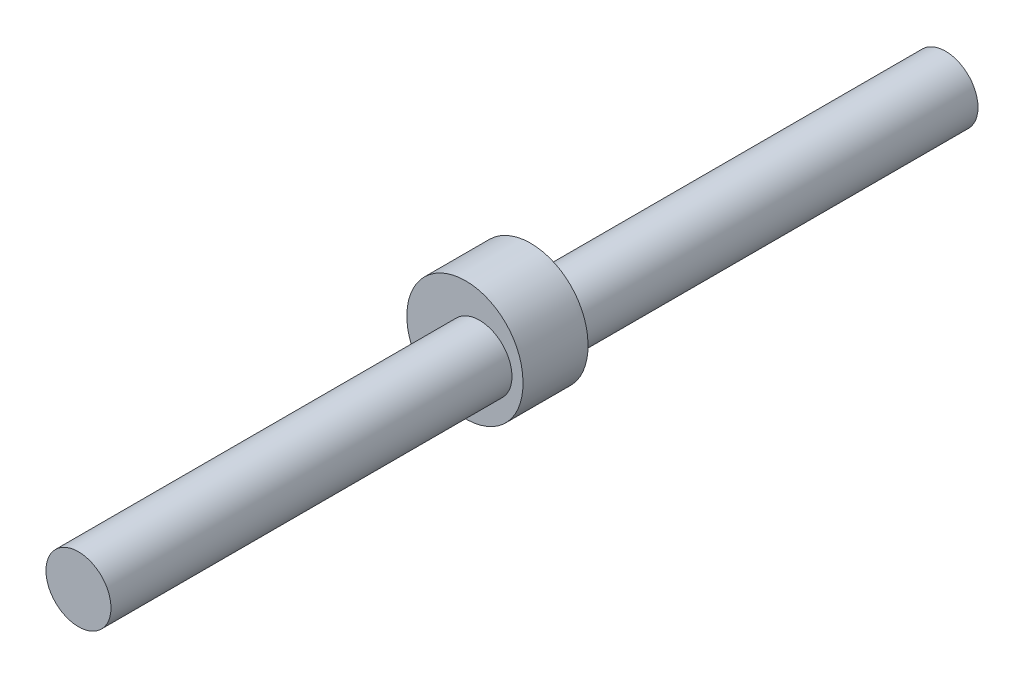
SolidWorks part; units mm, degrees
ref_plane "Front Plane" through (0, 0, 0) normal (0, 0, 1) x (1, 0, 0)
ref_plane "Top Plane" through (0, 0, 0) normal (0, 1, 0) x (1, 0, 0)
ref_plane "Right Plane" through (0, 0, 0) normal (1, 0, 0) x (0, 0, -1)
sketch "Sketch2" plane through (0, 0, 0) normal (0, 0, 1) x (1, 0, 0)
  spline S1 degree 3 poles (20.1005, -0.1773) (20.0999, -0.0008) (20.0997, 0.1756) (20.0981, 0.3513) (20.0956, 0.5269) (20.092, 0.7026) (20.0874, 0.8782) (20.0817, 1.0539) (20.0751, 1.2295) (20.0674, 1.4052) (20.0586, 1.5808) (20.0489, 1.7565) (20.0381, 1.9321) (20.0263, 2.1078) (20.0134, 2.2834) (19.9995, 2.4591) (19.9846, 2.6347) (19.9686, 2.8103) (19.9516, 2.986) (19.9335, 3.1616) (19.9144, 3.3372) (19.8942, 3.5128) (19.873, 3.6884) (19.8507, 3.864) (19.8273, 4.0396) (19.8029, 4.2152) (19.7775, 4.3908) (19.7509, 4.5664) (19.7233, 4.7419) (19.6946, 4.9175) (19.6648, 5.093) (19.6339, 5.2685) (19.6019, 5.444) (19.5689, 5.6194) (19.5347, 5.7949) (19.4994, 5.9703) (19.463, 6.1457) (19.4256, 6.321) (19.3869, 6.4964) (19.3472, 6.6717) (19.3063, 6.8469) (19.2643, 7.0221) (19.2212, 7.1973) (19.1769, 7.3724) (19.1314, 7.5475) (19.0848, 7.7225) (19.0371, 7.8975) (18.9881, 8.0724) (18.938, 8.2472) (18.8868, 8.422) (18.8343, 8.5967) (18.7806, 8.7713) (18.7258, 8.9458) (18.6697, 9.1203) (18.6126, 9.2947) (18.5529, 9.4702) (18.4951, 9.6468) (18.4343, 9.8209) (18.3699, 9.9923) (18.3078, 10.1649) (18.243, 10.3385) (18.1771, 10.512) (18.1099, 10.6854) (18.0415, 10.8587) (17.9717, 11.0318) (17.9007, 11.2048) (17.8284, 11.3776) (17.7548, 11.5502) (17.6799, 11.7226) (17.6037, 11.8948) (17.5262, 12.0669) (17.4474, 12.2387) (17.3673, 12.4103) (17.2858, 12.5817) (17.2029, 12.7529) (17.1188, 12.9238) (17.0332, 13.0945) (16.9463, 13.2649) (16.8581, 13.435) (16.7685, 13.6049) (16.6775, 13.7744) (16.5851, 13.9437) (16.4913, 14.1127) (16.3961, 14.2813) (16.2995, 14.4496) (16.2016, 14.6176) (16.1022, 14.7852) (16.0013, 14.9524) (15.8991, 15.1193) (15.7954, 15.2858) (15.6903, 15.4518) (15.5838, 15.6175) (15.4758, 15.7827) (15.3663, 15.9475) (15.2554, 16.1119) (15.1431, 16.2757) (15.0292, 16.4391) (14.9139, 16.602) (14.7971, 16.7644) (14.6789, 16.9263) (14.5591, 17.0877) (14.4379, 17.2484) (14.3152, 17.4087) (14.191, 17.5683) (14.0652, 17.7274) (13.938, 17.8858) (13.8093, 18.0437) (13.6791, 18.2009) (13.5473, 18.3574) (13.414, 18.5133) (13.2793, 18.6684) (13.143, 18.8229) (13.0051, 18.9767) (12.8658, 19.1297) (12.7249, 19.282) (12.5825, 19.4335) (12.4386, 19.5842) (12.2931, 19.7341) (12.1461, 19.8832) (11.9976, 20.0315) (11.8475, 20.1789) (11.6959, 20.3254) (11.5428, 20.4711) (11.3881, 20.6158) (11.2319, 20.7596) (11.0742, 20.9025) (10.915, 21.0444) (10.7542, 21.1853) (10.5919, 21.3253) (10.428, 21.4642) (10.2627, 21.602) (10.0958, 21.7389) (9.9274, 21.8746) (9.7574, 22.0093) (9.586, 22.1428) (9.413, 22.2752) (9.2386, 22.4065) (9.0626, 22.5365) (8.8852, 22.6654) (8.7062, 22.7931) (8.5258, 22.9196) (8.3438, 23.0448) (8.1604, 23.1687) (7.9755, 23.2914) (7.7892, 23.4127) (7.6014, 23.5327) (7.4121, 23.6514) (7.2214, 23.7687) (7.0292, 23.8846) (6.8356, 23.9991) (6.6405, 24.1122) (6.4441, 24.2238) (6.2462, 24.3339) (6.047, 24.4426) (5.8462, 24.5497) (5.6444, 24.6557) (5.4402, 24.7583) (5.2396, 24.8657) (5.0234, 24.9457) (4.8261, 25.0658) (4.613, 25.1587) (4.4035, 25.2563) (4.1919, 25.3502) (3.9792, 25.443) (3.7651, 25.534) (3.5498, 25.6232) (3.3332, 25.7107) (3.1153, 25.7964) (2.8962, 25.8804) (2.6759, 25.9625) (2.4544, 26.0428) (2.2317, 26.1213) (2.0078, 26.1979) (1.7828, 26.2726) (1.5566, 26.3454) (1.3292, 26.4163) (1.1007, 26.4853) (0.8712, 26.5523) (0.6405, 26.6173) (0.4088, 26.6803) (0.176, 26.7414) (-0.0578, 26.8003) (-0.2926, 26.8573) (-0.5284, 26.9121) (-0.7653, 26.9649) (-1.003, 27.0156) (-1.2417, 27.0642) (-1.4814, 27.1106) (-1.7219, 27.1549) (-1.9634, 27.197) (-2.2056, 27.2369) (-2.4488, 27.2746) (-2.6927, 27.3102) (-2.9375, 27.3434) (-3.183, 27.3744) (-3.4293, 27.4032) (-3.6764, 27.4297) (-3.9241, 27.4538) (-4.1726, 27.4757) (-4.4217, 27.4953) (-4.6714, 27.5125) (-4.9218, 27.5273) (-5.1728, 27.5398) (-5.4244, 27.5499) (-5.6765, 27.5576) (-5.9291, 27.5629) (-6.1822, 27.5658) (-6.4358, 27.5663) (-6.6899, 27.5643) (-6.9444, 27.5599) (-7.1993, 27.553) (-7.4546, 27.5436) (-7.7102, 27.5317) (-7.9661, 27.5173) (-8.2224, 27.5004) (-8.4789, 27.481) (-8.7356, 27.4591) (-8.9926, 27.4346) (-9.2497, 27.4076) (-9.507, 27.3781) (-9.7645, 27.3459) (-10.022, 27.3112) (-10.2796, 27.2739) (-10.5373, 27.234) (-10.795, 27.1916) (-11.0527, 27.1465) (-11.3103, 27.0988) (-11.5679, 27.0485) (-11.8254, 26.9956) (-12.0827, 26.9401) (-12.3399, 26.8819) (-12.5969, 26.8211) (-12.8537, 26.7577) (-13.1103, 26.6916) (-13.3665, 26.6229) (-13.6225, 26.5515) (-13.8781, 26.4775) (-14.1334, 26.4009) (-14.3883, 26.3215) (-14.6427, 26.2396) (-14.8967, 26.1549) (-15.1502, 26.0676) (-15.4032, 25.9777) (-15.6556, 25.8851) (-15.9074, 25.7899) (-16.1586, 25.692) (-16.4092, 25.5914) (-16.6591, 25.4882) (-16.9083, 25.3823) (-17.1568, 25.2738) (-17.4045, 25.1627) (-17.6514, 25.0489) (-17.8974, 24.9325) (-18.1426, 24.8135) (-18.3869, 24.6918) (-18.6303, 24.5675) (-18.8727, 24.4406) (-19.1142, 24.3111) (-19.3546, 24.179) (-19.5939, 24.0443) (-19.8322, 23.907) (-20.0694, 23.7671) (-20.3054, 23.6247) (-20.5402, 23.4797) (-20.7738, 23.3321) (-21.0062, 23.182) (-21.2373, 23.0294) (-21.4671, 22.8742) (-21.6956, 22.7166) (-21.9227, 22.5564) (-22.1485, 22.3938) (-22.3728, 22.2286) (-22.5956, 22.061) (-22.817, 21.891) (-23.0368, 21.7185) (-23.2551, 21.5436) (-23.4718, 21.3663) (-23.6869, 21.1865) (-23.9004, 21.0045) (-24.1122, 20.82) (-24.3223, 20.6332) (-24.5307, 20.444) (-24.7374, 20.2526) (-24.9422, 20.0588) (-25.1453, 19.8628) (-25.3465, 19.6645) (-25.5458, 19.4639) (-25.7433, 19.2612) (-25.9388, 19.0562) (-26.1324, 18.849) (-26.324, 18.6397) (-26.5136, 18.4282) (-26.7011, 18.2146) (-26.8866, 17.9989) (-27.07, 17.7811) (-27.2513, 17.5612) (-27.4305, 17.3393) (-27.6075, 17.1154) (-27.7823, 16.8895) (-27.9548, 16.6616) (-28.1252, 16.4317) (-28.2933, 16.2) (-28.459, 15.9663) (-28.6225, 15.7308) (-28.7836, 15.4934) (-28.9424, 15.2542) (-29.0988, 15.0131) (-29.2528, 14.7704) (-29.4043, 14.5258) (-29.5534, 14.2796) (-29.7, 14.0316) (-29.8442, 13.782) (-29.9858, 13.5308) (-30.1248, 13.2779) (-30.2614, 13.0235) (-30.3953, 12.7675) (-30.5266, 12.5099) (-30.6553, 12.2509) (-30.7814, 11.9904) (-30.9048, 11.7285) (-31.0256, 11.4652) (-31.1436, 11.2005) (-31.2589, 10.9344) (-31.3715, 10.6671) (-31.4814, 10.3984) (-31.5885, 10.1285) (-31.6928, 9.8574) (-31.7944, 9.5851) (-31.8931, 9.3116) (-31.989, 9.037) (-32.082, 8.7613) (-32.1722, 8.4845) (-32.2596, 8.2067) (-32.344, 7.9279) (-32.4256, 7.6482) (-32.5043, 7.3675) (-32.58, 7.0859) (-32.6528, 6.8035) (-32.7227, 6.5202) (-32.7897, 6.2361) (-32.8536, 5.9513) (-32.9146, 5.6658) (-32.9727, 5.3795) (-33.0277, 5.0926) (-33.0797, 4.8051) (-33.1288, 4.517) (-33.1748, 4.2283) (-33.2178, 3.9391) (-33.2578, 3.6494) (-33.2948, 3.3593) (-33.3287, 3.0688) (-33.3596, 2.7779) (-33.3874, 2.4866) (-33.4122, 2.195) (-33.4339, 1.9032) (-33.4526, 1.6111) (-33.4682, 1.3188) (-33.4807, 1.0264) (-33.4902, 0.7338) (-33.4966, 0.4412) (-33.4999, 0.1484) (-33.5002, -0.1443) (-33.4974, -0.437) (-33.4915, -0.7297) (-33.4826, -1.0223) (-33.4706, -1.3148) (-33.4556, -1.6071) (-33.4374, -1.8992) (-33.4163, -2.1911) (-33.392, -2.4828) (-33.3647, -2.7741) (-33.3344, -3.0651) (-33.301, -3.3558) (-33.2646, -3.646) (-33.2251, -3.9358) (-33.1827, -4.2251) (-33.1372, -4.5139) (-33.0886, -4.8022) (-33.0371, -5.0899) (-32.9826, -5.377) (-32.9251, -5.6634) (-32.8646, -5.9491) (-32.8012, -6.2341) (-32.7347, -6.5184) (-32.6653, -6.8019) (-32.593, -7.0845) (-32.5178, -7.3663) (-32.4396, -7.6472) (-32.3585, -7.9272) (-32.2745, -8.2063) (-32.1877, -8.4843) (-32.098, -8.7613) (-32.0054, -9.0373) (-31.9099, -9.3122) (-31.8117, -9.586) (-31.7106, -9.8586) (-31.6067, -10.13) (-31.5001, -10.4002) (-31.3907, -10.6692) (-31.2785, -10.9369) (-31.1636, -11.2033) (-31.046, -11.4684) (-30.9256, -11.732) (-30.8026, -11.9943) (-30.677, -12.2552) (-30.5487, -12.5146) (-30.4177, -12.7725) (-30.2842, -13.0288) (-30.148, -13.2837) (-30.0093, -13.5369) (-29.8681, -13.7886) (-29.7243, -14.0386) (-29.5781, -14.287) (-29.4293, -14.5336) (-29.2781, -14.7786) (-29.1245, -15.0218) (-28.9684, -15.2633) (-28.8099, -15.5029) (-28.6491, -15.7408) (-28.4859, -15.9768) (-28.3204, -16.2109) (-28.1526, -16.4431) (-27.9826, -16.6734) (-27.8103, -16.9018) (-27.6357, -17.1282) (-27.459, -17.3526) (-27.2801, -17.575) (-27.099, -17.7953) (-26.9158, -18.0136) (-26.7306, -18.2298) (-26.5432, -18.4439) (-26.3538, -18.6559) (-26.1624, -18.8658) (-25.969, -19.0734) (-25.7737, -19.2789) (-25.5764, -19.4822) (-25.3772, -19.6833) (-25.1762, -19.8821) (-24.9732, -20.0787) (-24.7685, -20.273) (-24.562, -20.4649) (-24.3537, -20.6546) (-24.1437, -20.8419) (-23.932, -21.0269) (-23.7186, -21.2096) (-23.5035, -21.3898) (-23.2869, -21.5677) (-23.0686, -21.7431) (-22.8488, -21.9161) (-22.6275, -22.0867) (-22.4047, -22.2549) (-22.1804, -22.4205) (-21.9547, -22.5837) (-21.7276, -22.7444) (-21.4991, -22.9026) (-21.2693, -23.0583) (-21.0381, -23.2115) (-20.8057, -23.3621) (-20.5721, -23.5102) (-20.3372, -23.6558) (-20.1011, -23.7987) (-19.8639, -23.9391) (-19.6255, -24.077) (-19.3861, -24.2122) (-19.1456, -24.3448) (-18.904, -24.4749) (-18.6615, -24.6023) (-18.418, -24.7271) (-18.1736, -24.8493) (-17.9282, -24.9688) (-17.682, -25.0858) (-17.4349, -25.2001) (-17.1871, -25.3117) (-16.9384, -25.4207) (-16.6891, -25.5271) (-16.439, -25.6308) (-16.1882, -25.7318) (-15.9367, -25.8302) (-15.6847, -25.9259) (-15.432, -26.019) (-15.1788, -26.1094) (-14.9251, -26.1972) (-14.6708, -26.2823) (-14.4161, -26.3647) (-14.161, -26.4445) (-13.9054, -26.5216) (-13.6495, -26.5961) (-13.3933, -26.6679) (-13.1367, -26.7371) (-12.8798, -26.8036) (-12.6227, -26.8674) (-12.3654, -26.9286) (-12.1079, -26.9872) (-11.8502, -27.0432) (-11.5924, -27.0965) (-11.3345, -27.1472) (-11.0765, -27.1953) (-10.8184, -27.2407) (-10.5604, -27.2836) (-10.3023, -27.3238) (-10.0443, -27.3615) (-9.7864, -27.3965) (-9.5285, -27.429) (-9.2708, -27.4589) (-9.0133, -27.4863) (-8.7559, -27.5111) (-8.4987, -27.5334) (-8.2418, -27.5531) (-7.9851, -27.5703) (-7.7288, -27.5849) (-7.4727, -27.5971) (-7.217, -27.6068) (-6.9617, -27.614) (-6.7067, -27.6187) (-6.4522, -27.6209) (-6.1981, -27.6207) (-5.9445, -27.6181) (-5.6914, -27.613) (-5.4389, -27.6055) (-5.1868, -27.5956) (-4.9354, -27.5834) (-4.6845, -27.5687) (-4.4343, -27.5517) (-4.1847, -27.5323) (-3.9357, -27.5106) (-3.6875, -27.4866) (-3.4399, -27.4603) (-3.1931, -27.4317) (-2.9471, -27.4008) (-2.7018, -27.3677) (-2.4574, -27.3323) (-2.2137, -27.2947) (-1.9709, -27.2549) (-1.729, -27.2129) (-1.4879, -27.1687) (-1.2478, -27.1224) (-1.0085, -27.0739) (-0.7703, -27.0233) (-0.5329, -26.9705) (-0.2966, -26.9157) (-0.0612, -26.8588) (0.1731, -26.7998) (0.4064, -26.7388) (0.6386, -26.6758) (0.8698, -26.6108) (1.0999, -26.5438) (1.3289, -26.4748) (1.5567, -26.4039) (1.7834, -26.331) (2.009, -26.2563) (2.2334, -26.1796) (2.4567, -26.1011) (2.6787, -26.0207) (2.8995, -25.9385) (3.1191, -25.8545) (3.3374, -25.7686) (3.5545, -25.681) (3.7704, -25.5917) (3.9849, -25.5006) (4.1982, -25.4078) (4.4101, -25.3133) (4.6208, -25.2171) (4.8301, -25.1192) (5.0381, -25.0197) (5.2447, -24.9186) (5.45, -24.816) (5.6539, -24.7117) (5.8564, -24.6059) (6.0576, -24.4985) (6.2573, -24.3896) (6.4556, -24.2792) (6.6525, -24.1674) (6.848, -24.0541) (7.0421, -23.9393) (7.2347, -23.8232) (7.4258, -23.7056) (7.6156, -23.5867) (7.8038, -23.4664) (7.9906, -23.3447) (8.1759, -23.2218) (8.3597, -23.0976) (8.542, -22.9721) (8.7229, -22.8453) (8.9022, -22.7173) (9.0801, -22.5881) (9.2564, -22.4576) (9.4313, -22.326) (9.6046, -22.1933) (9.7764, -22.0594) (9.9467, -21.9244) (10.1154, -21.7883) (10.2827, -21.6511) (10.4484, -21.5128) (10.6125, -21.3735) (10.7752, -21.2332) (10.9363, -21.0919) (11.0958, -20.9496) (11.2539, -20.8063) (11.4103, -20.6621) (11.5653, -20.5169) (11.7187, -20.3709) (11.8706, -20.2239) (12.0209, -20.0761) (12.1697, -19.9274) (12.3169, -19.7778) (12.4626, -19.6275) (12.6068, -19.4763) (12.7494, -19.3244) (12.8905, -19.1716) (13.0301, -19.0182) (13.1681, -18.8639) (13.3046, -18.709) (13.4396, -18.5533) (13.573, -18.397) (13.7049, -18.24) (13.8353, -18.0823) (13.9642, -17.924) (14.0916, -17.7651) (14.2174, -17.6056) (14.3418, -17.4454) (14.4646, -17.2847) (14.586, -17.1234) (14.7058, -16.9616) (14.8242, -16.7992) (14.941, -16.6363) (15.0564, -16.4729) (15.1703, -16.3091) (15.2827, -16.1447) (15.3937, -15.9799) (15.5031, -15.8146) (15.6112, -15.6488) (15.7177, -15.4827) (15.8229, -15.3161) (15.9265, -15.1491) (16.0288, -14.9818) (16.1296, -14.814) (16.2289, -14.6459) (16.3269, -14.4775) (16.4234, -14.3087) (16.5185, -14.1395) (16.6123, -13.9701) (16.7046, -13.8003) (16.7955, -13.6303) (16.885, -13.4599) (16.9732, -13.2893) (17.06, -13.1184) (17.1454, -12.9472) (17.2295, -12.7758) (17.3122, -12.6042) (17.3935, -12.4323) (17.4735, -12.2602) (17.5522, -12.0879) (17.6295, -11.9154) (17.7056, -11.7427) (17.7803, -11.5698) (17.8537, -11.3968) (17.9258, -11.2235) (17.9966, -11.0501) (18.0661, -10.8766) (18.1343, -10.7029) (18.2013, -10.529) (18.267, -10.3551) (18.3314, -10.181) (18.3946, -10.0067) (18.4565, -9.8324) (18.5172, -9.6579) (18.5766, -9.4834) (18.6348, -9.3087) (18.6918, -9.1339) (18.7476, -8.9591) (18.8021, -8.7842) (18.8555, -8.6092) (18.9076, -8.4341) (18.9586, -8.259) (19.0084, -8.0838) (19.057, -7.9085) (19.1044, -7.7332) (19.1507, -7.5578) (19.1957, -7.3824) (19.2397, -7.207) (19.2825, -7.0315) (19.3241, -6.8559) (19.3646, -6.6804) (19.404, -6.5048) (19.4422, -6.3291) (19.4793, -6.1535) (19.5153, -5.9778) (19.5501, -5.8021) (19.5839, -5.6264) (19.6166, -5.4507) (19.6481, -5.2749) (19.6786, -5.0992) (19.7079, -4.9234) (19.7362, -4.7476) (19.7634, -4.5718) (19.7895, -4.3961) (19.8145, -4.2203) (19.8385, -4.0445) (19.8614, -3.8687) (19.8832, -3.6929) (19.904, -3.5171) (19.9237, -3.3413) (19.9424, -3.1655) (19.96, -2.9897) (19.9765, -2.814) (19.9921, -2.6382) (20.0065, -2.4624) (20.0199, -2.2867) (20.0323, -2.1109) (20.0437, -1.9352) (20.054, -1.7594) (20.0633, -1.5837) (20.0715, -1.408) (20.0787, -1.2323) (20.0849, -1.0566) (20.09, -0.8809) (20.0956, -0.6466) (20.0989, -0.4124) (20.1005, -0.1773) (20.0999, -0.0008) (20.0997, 0.1756) knots -0.004122 -0.002068 -0.001041 0 0.001027 0.002053 0.00308 0.004107 0.005134 0.006161 0.007189 0.008216 0.009244 0.010272 0.011301 0.01233 0.013359 0.014389 0.015419 0.01645 0.017482 0.018514 0.019546 0.020579 0.021613 0.022648 0.023683 0.024719 0.025756 0.026794 0.027833 0.028873 0.029913 0.030955 0.031997 0.033041 0.034086 0.035132 0.036179 0.037227 0.038276 0.039327 0.040378 0.041432 0.042486 0.043542 0.044599 0.045658 0.046718 0.047779 0.048842 0.049907 0.050973 0.052041 0.05311 0.054181 0.055254 0.056328 0.057433 0.058511 0.059562 0.060643 0.061727 0.062812 0.063899 0.064988 0.066078 0.067171 0.068266 0.069363 0.070461 0.071562 0.072665 0.07377 0.074877 0.075986 0.077098 0.078212 0.079327 0.080445 0.081566 0.082688 0.083813 0.08494 0.08607 0.087202 0.088336 0.089472 0.090611 0.091753 0.092897 0.094043 0.095192 0.096343 0.097497 0.098653 0.099812 0.100973 0.102137 0.103304 0.104473 0.105645 0.106819 0.107996 0.109176 0.110358 0.111543 0.112731 0.113921 0.115114 0.11631 0.117509 0.11871 0.119914 0.121121 0.122331 0.123544 0.124759 0.125977 0.127198 0.128422 0.129648 0.130878 0.13211 0.133346 0.134584 0.135825 0.137068 0.138315 0.139565 0.140818 0.142073 0.143331 0.144593 0.145857 0.147124 0.148395 0.149668 0.150944 0.152223 0.153505 0.15479 0.156078 0.157368 0.158662 0.159959 0.161259 0.162562 0.163867 0.165176 0.166488 0.167803 0.16912 0.170441 0.171765 0.173091 0.174421 0.175754 0.177089 0.178428 0.179741 0.181116 0.182464 0.183814 0.185168 0.186524 0.187884 0.189246 0.190612 0.19198 0.193351 0.194725 0.196103 0.197483 0.198866 0.200252 0.201641 0.203033 0.204428 0.205826 0.207226 0.20863 0.210037 0.211446 0.212858 0.214274 0.215692 0.217113 0.218537 0.219963 0.221393 0.222825 0.224261 0.225699 0.22714 0.228583 0.23003 0.231479 0.232932 0.234387 0.235844 0.237305 0.238768 0.240234 0.241703 0.243175 0.244649 0.246126 0.247605 0.249088 0.250573 0.252061 0.253551 0.255044 0.25654 0.258038 0.259539 0.261042 0.262549 0.264057 0.265569 0.267082 0.268599 0.270118 0.271639 0.273163 0.27469 0.276219 0.27775 0.279284 0.280821 0.28236 0.283901 0.285444 0.28699 0.288539 0.29009 0.291643 0.293198 0.294756 0.296317 0.297879 0.299444 0.301011 0.30258 0.304152 0.305725 0.307301 0.30888 0.31046 0.312042 0.313627 0.315214 0.316803 0.318394 0.319987 0.321582 0.32318 0.324779 0.32638 0.327984 0.329589 0.331196 0.332806 0.334417 0.33603 0.337645 0.339262 0.340881 0.342502 0.344124 0.345749 0.347375 0.349003 0.350633 0.352264 0.353897 0.355532 0.357169 0.358807 0.360447 0.362089 0.363733 0.365377 0.367024 0.368672 0.370322 0.371973 0.373626 0.37528 0.376936 0.378593 0.380252 0.381912 0.383573 0.385236 0.386901 0.388566 0.390233 0.391901 0.393571 0.395242 0.396914 0.398587 0.400262 0.401938 0.403615 0.405293 0.406972 0.408653 0.410334 0.412017 0.4137 0.415385 0.417071 0.418758 0.420445 0.422134 0.423824 0.425514 0.427206 0.428898 0.430591 0.432285 0.43398 0.435676 0.437373 0.43907 0.440768 0.442467 0.444166 0.445866 0.447567 0.449268 0.45097 0.452673 0.454376 0.45608 0.457784 0.459489 0.461194 0.4629 0.464607 0.466313 0.46802 0.469728 0.471436 0.473144 0.474853 0.476562 0.478271 0.47998 0.48169 0.4834 0.48511 0.48682 0.488531 0.490242 0.491952 0.493663 0.495374 0.497085 0.498796 0.500507 0.502218 0.503929 0.50564 0.507351 0.509062 0.510773 0.512484 0.514194 0.515905 0.517615 0.519325 0.521034 0.522744 0.524453 0.526162 0.527871 0.529579 0.531287 0.532994 0.534701 0.536408 0.538114 0.53982 0.541526 0.54323 0.544935 0.546638 0.548342 0.550044 0.551746 0.553448 0.555149 0.556849 0.558548 0.560247 0.561945 0.563642 0.565339 0.567034 0.568729 0.570423 0.572116 0.573809 0.5755 0.577191 0.578881 0.580569 0.582257 0.583944 0.585629 0.587314 0.588998 0.59068 0.592362 0.594042 0.595722 0.5974 0.599077 0.600753 0.602427 0.604101 0.605773 0.607444 0.609113 0.610781 0.612448 0.614114 0.615778 0.617441 0.619103 0.620763 0.622422 0.624079 0.625735 0.627389 0.629042 0.630693 0.632342 0.633991 0.635637 0.637282 0.638925 0.640567 0.642207 0.643846 0.645482 0.647117 0.648751 0.650382 0.652012 0.65364 0.655266 0.65689 0.658513 0.660134 0.661753 0.66337 0.664985 0.666598 0.668209 0.669818 0.671426 0.673031 0.674634 0.676236 0.677835 0.679432 0.681028 0.682621 0.684212 0.685801 0.687388 0.688972 0.690555 0.692135 0.693713 0.695289 0.696863 0.698435 0.700004 0.701571 0.703136 0.704698 0.706258 0.707816 0.709372 0.710925 0.712476 0.714024 0.71557 0.717114 0.718655 0.720194 0.72173 0.723264 0.724796 0.726325 0.727851 0.729375 0.730897 0.732416 0.733932 0.735446 0.736957 0.738466 0.739972 0.741476 0.742977 0.744475 0.745971 0.747464 0.748954 0.750442 0.751927 0.753409 0.754889 0.756366 0.75784 0.759312 0.76078 0.762246 0.76371 0.76517 0.766628 0.768083 0.769535 0.770985 0.772431 0.773875 0.775316 0.776754 0.778189 0.779622 0.781051 0.782478 0.783902 0.785323 0.786741 0.788156 0.789569 0.790978 0.792385 0.793788 0.795189 0.796587 0.797982 0.799374 0.800763 0.802149 0.803532 0.804912 0.806289 0.807663 0.809035 0.810403 0.811768 0.813131 0.81449 0.815847 0.8172 0.818551 0.819898 0.821243 0.822585 0.823923 0.825259 0.826591 0.827921 0.829248 0.830571 0.831892 0.83321 0.834524 0.835836 0.837145 0.838451 0.839753 0.841053 0.84235 0.843644 0.844935 0.846223 0.847508 0.84879 0.850069 0.851345 0.852618 0.853888 0.855155 0.85642 0.857681 0.858939 0.860195 0.861447 0.862697 0.863944 0.865188 0.866429 0.867667 0.868902 0.870134 0.871364 0.872591 0.873814 0.875035 0.876253 0.877469 0.878681 0.879891 0.881098 0.882302 0.883503 0.884702 0.885898 0.887091 0.888282 0.889469 0.890654 0.891837 0.893016 0.894193 0.895368 0.89654 0.897709 0.898875 0.900039 0.901201 0.902359 0.903516 0.904669 0.905821 0.90697 0.908116 0.90926 0.910401 0.91154 0.912677 0.913811 0.914943 0.916072 0.917199 0.918324 0.919447 0.920567 0.921685 0.922801 0.923914 0.925026 0.926135 0.927242 0.928347 0.92945 0.930551 0.93165 0.932746 0.933841 0.934934 0.936025 0.937114 0.938201 0.939286 0.940369 0.94145 0.94253 0.943608 0.944684 0.945758 0.946831 0.947902 0.948971 0.950039 0.951105 0.95217 0.953233 0.954294 0.955354 0.956413 0.95747 0.958526 0.959581 0.960634 0.961686 0.962736 0.963785 0.964834 0.965881 0.966926 0.967971 0.969015 0.970057 0.971099 0.972139 0.973179 0.974218 0.975256 0.976293 0.977329 0.978364 0.979399 0.980433 0.981466 0.982499 0.983531 0.984562 0.985593 0.986623 0.987653 0.988682 0.989711 0.99074 0.991768 0.992796 0.993824 0.994851 0.995878 0.997932 0.998959 1 1.001027 1.002053 1.00308 only from (20.1, 0) to (20.1, 0)
extrude "Boss-Extrude1" add sketch "Sketch2" along normal mid plane 30
sketch "Sketch3" plane through (0, 0, 15) normal (0, 0, 1) x (1, 0, 0)
  circle A0 centre (0, 0) radius 15
extrude "Boss-Extrude2" add sketch "Sketch3" along normal blind 185
mirror "Mirror1" about plane through (0, 0, 0) normal (0, 0, 1) of "Boss-Extrude2"
